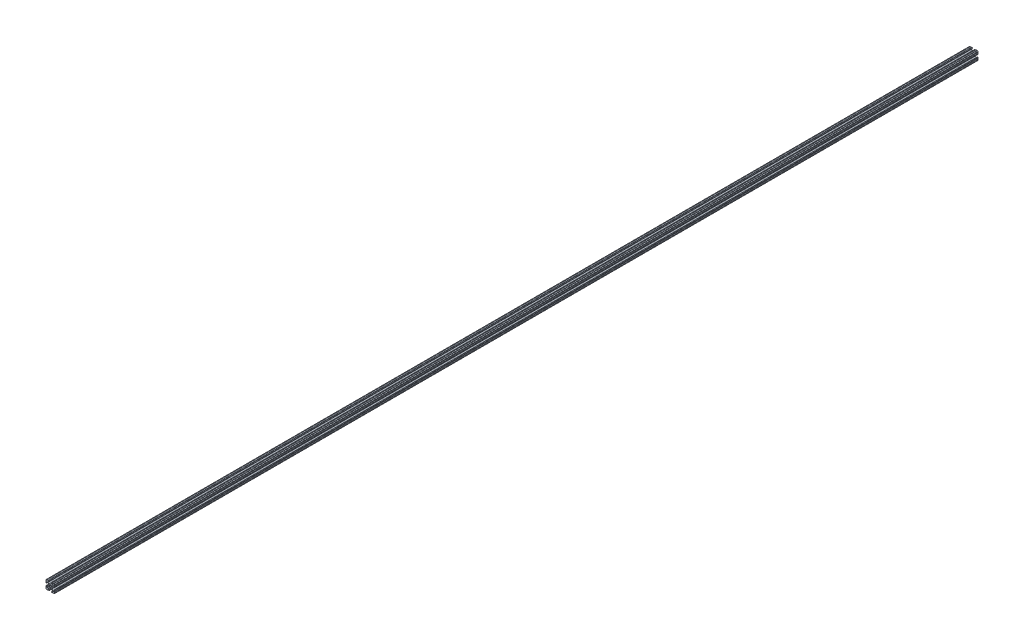
SolidWorks part; units mm, degrees
ref_plane "Front Plane" through (0, 0, 0) normal (0, 0, 1) x (1, 0, 0)
ref_plane "Top Plane" through (0, 0, 0) normal (0, 1, 0) x (1, 0, 0)
ref_plane "Right Plane" through (0, 0, 0) normal (1, 0, 0) x (0, 0, -1)
sketch "Sketch1" plane through (0, 0, 0) normal (0, 0, 1) x (1, 0, 0)
  line L0 (0, -12.7) -> (0, 12.7) construction
  line L1 (12.7, 0) -> (-12.7, 0) construction
  line L2 (3.2512, 12.7) -> (-3.2512, 12.7) construction
  line L3 (0, -4.5212) -> (0, 4.5212) construction
  line L4 (-3.2512, 12.7) -> (-3.2512, 10.4902) construction
  line L5 (12.7, -7.4168) -> (12.7, 7.4168) construction
  line L6 (0, -2.6035) -> (0, 2.6035) construction
  point P4 (0, 0)
  point P8 (0, 0)
  point P11 (0, 12.7)
  point P14 (0, 0)
  point P18 (12.7, 0)
  point P21 (0, 0)
sketch "Sketch2" plane through (0, 0, 0) normal (1, 0, 0) x (0, 0, -1)
  line L0 (-1371.6, 0) -> (1371.6, 0) construction
  point P4 (0, 0)
  dimension "Length" = 2743.2
sketch "Sketch3" plane through (0, 0, 0) normal (0, 0, 1) x (1, 0, 0)
  line L1 (12.7, -12.7) -> (-12.7, -12.7)
  line L2 (12.7, -12.7) -> (12.7, 12.7)
  line L3 (12.7, 12.7) -> (-12.7, 12.7)
  line L4 (-12.7, -12.7) -> (-12.7, 12.7)
  line L5 (12.7, -12.7) -> (-12.7, 12.7) construction
  line L6 (12.7, 12.7) -> (-12.7, -12.7) construction
  point P0 (0, 0)
extrude "Boss-Extrude1" add sketch "Sketch3" along normal up to vertex (1371.6 mm away) and the other way up to vertex (1371.6 mm away) up to point (0, 0, 1371.6) other way up to point (0, 0, -1371.6)
sketch "Sketch4" plane through (0, 0, 1371.6) normal (0, 0, 1) x (1, 0, 0)
  line L0 (-3.2512, 12.7) -> (-3.2512, 10.4902)
  line L1 (-3.2512, 10.4902) -> (-8.9276, 10.4902)
  line L2 (-8.9276, 10.4902) -> (-2.9586, 4.5212)
  line L3 (-2.9586, 4.5212) -> (2.9586, 4.5212)
  line L4 (0, -12.7) -> (0, 12.7) construction
  line L5 (12.7, 12.7) -> (-12.7, 12.7) construction
  line L6 (0, 12.7) -> (0, -12.7) construction
  line L7 (-12.7, 0) -> (12.7, 0) construction
  line L8 (-12.7, 12.7) -> (0, 0) construction
  line L9 (-12.7, 3.2512) -> (-10.4902, 3.2512)
  line L10 (-10.4902, 3.2512) -> (-10.4902, 8.9276)
  line L11 (-10.4902, 8.9276) -> (-4.5212, 2.9586)
  line L12 (-4.5212, 2.9586) -> (-4.5212, -2.9586)
  line L13 (4.5212, 2.9586) -> (4.5212, -2.9586)
  line L14 (10.4902, 8.9276) -> (4.5212, 2.9586)
  line L15 (10.4902, 3.2512) -> (10.4902, 8.9276)
  line L16 (12.7, 3.2512) -> (10.4902, 3.2512)
  line L17 (8.9276, 10.4902) -> (2.9586, 4.5212)
  line L18 (3.2512, 10.4902) -> (8.9276, 10.4902)
  line L19 (3.2512, 12.7) -> (3.2512, 10.4902)
  line L20 (3.2512, -12.7) -> (3.2512, -10.4902)
  line L21 (3.2512, -10.4902) -> (8.9276, -10.4902)
  line L22 (8.9276, -10.4902) -> (2.9586, -4.5212)
  line L23 (12.7, -3.2512) -> (10.4902, -3.2512)
  line L24 (10.4902, -3.2512) -> (10.4902, -8.9276)
  line L25 (10.4902, -8.9276) -> (4.5212, -2.9586)
  line L26 (-10.4902, -8.9276) -> (-4.5212, -2.9586)
  line L27 (-10.4902, -3.2512) -> (-10.4902, -8.9276)
  line L28 (-12.7, -3.2512) -> (-10.4902, -3.2512)
  line L29 (-2.9586, -4.5212) -> (2.9586, -4.5212)
  line L30 (-8.9276, -10.4902) -> (-2.9586, -4.5212)
  line L31 (-3.2512, -10.4902) -> (-8.9276, -10.4902)
  line L32 (-3.2512, -12.7) -> (-3.2512, -10.4902)
  line L33 (-12.7, 3.2512) -> (-12.7, -3.2512)
  line L34 (-3.2512, -12.7) -> (3.2512, -12.7)
  line L35 (12.7, -3.2512) -> (12.7, 3.2512)
  line L36 (3.2512, 12.7) -> (-3.2512, 12.7)
  line L37 (-12.7, 12.7) -> (-12.7, -12.7) construction
  line L38 (-12.7, -12.7) -> (12.7, -12.7) construction
  arc A3 (-6.3485, 10.4902) -> (-7.1039, 8.6665) centre (-6.3485, 9.4219) ccw
  arc A4 (7.1039, 8.6665) -> (6.3485, 10.4902) centre (6.3485, 9.4219) ccw
  arc A5 (8.6665, -7.1039) -> (10.4902, -6.3485) centre (9.4219, -6.3485) ccw
  arc A6 (10.4902, 6.3485) -> (8.6665, 7.1039) centre (9.4219, 6.3485) ccw
  arc A7 (-7.1039, -8.6665) -> (-6.3485, -10.4902) centre (-6.3485, -9.4219) ccw
  arc A8 (6.3485, -10.4902) -> (7.1039, -8.6665) centre (6.3485, -9.4219) ccw
  arc A9 (-8.6665, 7.1039) -> (-10.4902, 6.3485) centre (-9.4219, 6.3485) ccw
  arc A10 (-10.4902, -6.3485) -> (-8.6665, -7.1039) centre (-9.4219, -6.3485) ccw
  circle A11 centre (0, 0) radius 2.6035
  point P34 (0, 4.5212)
  point P45 (4.5212, 0)
  point P46 (-4.5212, 0)
  point P53 (0, -4.5212)
  point P81 (0, 0)
  line M2 (-12.7, 12.7) -> (-12.7, -12.7)
  line M3 (-12.7, -12.7) -> (12.7, -12.7)
  line M4 (12.7, -12.7) -> (12.7, 12.7)
  line M5 (12.7, 12.7) -> (-12.7, 12.7)
  dimension "D5" = 5.207
  dimension "D1" = 2.2098
  dimension "D2" = 2.2098
  dimension "D3" = 14.8336
  dimension "D4" = 4
extrude "Cut-Extrude1" cut sketch "Sketch4" against normal through all contours L17 A4 L18 L19 L0 L1 A3 L2 L3 M5 | L15 A6 L14 L13 L25 A5 L24 L23 L16 M4 | L21 A8 L22 L29 L30 A7 L31 L32 L20 M3 | L27 A10 L26 L12 L11 A9 L10 L9 L28 M2 | A11
sketch "Sketch5" plane through (0, 0, 1371.6) normal (0, 0, 1) x (1, 0, 0)
  line L0 (-4.3561, 12.7) -> (-3.2512, 12.7)
  line L1 (-3.2512, 12.7) -> (-3.2512, 10.4902)
  line L2 (-3.2512, 10.4902) -> (-4.3561, 10.4902)
  line L3 (0, -12.7) -> (0, 12.7) construction
  line L4 (-3.2512, 12.7) -> (-12.7, 12.7) construction
  line L5 (3.2512, 10.4902) -> (4.3561, 10.4902)
  line L6 (3.2512, 12.7) -> (3.2512, 10.4902)
  line L7 (4.3561, 12.7) -> (3.2512, 12.7)
  line L8 (12.7, 4.3561) -> (12.7, 3.2512)
  line L9 (12.7, 3.2512) -> (10.4902, 3.2512)
  line L10 (10.4902, 3.2512) -> (10.4902, 4.3561)
  line L11 (10.4902, -3.2512) -> (10.4902, -4.3561)
  line L12 (12.7, -3.2512) -> (10.4902, -3.2512)
  line L13 (12.7, -4.3561) -> (12.7, -3.2512)
  line L14 (4.3561, -12.7) -> (3.2512, -12.7)
  line L15 (3.2512, -12.7) -> (3.2512, -10.4902)
  line L16 (3.2512, -10.4902) -> (4.3561, -10.4902)
  line L17 (-3.2512, -10.4902) -> (-4.3561, -10.4902)
  line L18 (-3.2512, -12.7) -> (-3.2512, -10.4902)
  line L19 (-4.3561, -12.7) -> (-3.2512, -12.7)
  line L20 (-12.7, -4.3561) -> (-12.7, -3.2512)
  line L21 (-12.7, -3.2512) -> (-10.4902, -3.2512)
  line L22 (-10.4902, -3.2512) -> (-10.4902, -4.3561)
  line L23 (-10.4902, 3.2512) -> (-10.4902, 4.3561)
  line L24 (-12.7, 3.2512) -> (-10.4902, 3.2512)
  line L25 (-12.7, 4.3561) -> (-12.7, 3.2512)
  line L26 (-12.7, 12.7) -> (-12.7, 3.2512) construction
  line L27 (-10.7124, 12.7) -> (-9.6075, 12.7)
  line L28 (-6.3436, 12.7) -> (-5.2387, 12.7)
  line L29 (-12.7, 10.7124) -> (-12.7, 9.6075)
  line L30 (-12.7, 6.3436) -> (-12.7, 5.2387)
  line L31 (6.3437, 12.7) -> (5.2388, 12.7)
  line L32 (10.7125, 12.7) -> (9.6076, 12.7)
  line L33 (12.7, 10.7125) -> (12.7, 9.6075)
  line L34 (12.7, 6.3436) -> (12.7, 5.2387)
  line L35 (12.7, -6.3437) -> (12.7, -5.2388)
  line L36 (12.7, -10.7125) -> (12.7, -9.6076)
  line L37 (10.7125, -12.7) -> (9.6076, -12.7)
  line L38 (6.3437, -12.7) -> (5.2388, -12.7)
  line L39 (-6.3436, -12.7) -> (-5.2387, -12.7)
  line L40 (-10.7124, -12.7) -> (-9.6075, -12.7)
  line L41 (-12.7, -10.7125) -> (-12.7, -9.6076)
  line L42 (-12.7, -6.3437) -> (-12.7, -5.2388)
  line L43 (12.7, 12.7) -> (3.2512, 12.7) construction
  line L44 (12.7, 3.2512) -> (12.7, 12.7) construction
  arc A0 (-4.3561, 10.4902) -> (-4.3561, 12.7) centre (-4.3561, 11.5951) ccw
  arc A1 (4.3561, 10.4902) -> (4.3561, 12.7) centre (4.3561, 11.5951) cw
  arc A2 (10.4902, 4.3561) -> (12.7, 4.3561) centre (11.5951, 4.3561) ccw
  arc A3 (10.4902, -4.3561) -> (12.7, -4.3561) centre (11.5951, -4.3561) cw
  arc A4 (4.3561, -10.4902) -> (4.3561, -12.7) centre (4.3561, -11.5951) ccw
  arc A5 (-4.3561, -10.4902) -> (-4.3561, -12.7) centre (-4.3561, -11.5951) cw
  arc A6 (-10.4902, -4.3561) -> (-12.7, -4.3561) centre (-11.5951, -4.3561) ccw
  arc A7 (-10.4902, 4.3561) -> (-12.7, 4.3561) centre (-11.5951, 4.3561) cw
  arc A8 (-10.7124, 12.7) -> (-9.6075, 12.7) centre (-10.16, 12.7) ccw
  arc A9 (-6.3436, 12.7) -> (-5.2387, 12.7) centre (-5.7912, 12.7) ccw
  arc A10 (-12.7, 9.6075) -> (-12.7, 10.7124) centre (-12.7, 10.16) ccw
  arc A11 (-12.7, 5.2387) -> (-12.7, 6.3436) centre (-12.7, 5.7912) ccw
  arc A12 (5.2388, 12.7) -> (6.3437, 12.7) centre (5.7912, 12.7) ccw
  arc A13 (9.6076, 12.7) -> (10.7125, 12.7) centre (10.16, 12.7) ccw
  arc A14 (12.7, 10.7125) -> (12.7, 9.6075) centre (12.7, 10.16) ccw
  arc A15 (12.7, 6.3436) -> (12.7, 5.2387) centre (12.7, 5.7912) ccw
  arc A16 (12.7, -5.2388) -> (12.7, -6.3437) centre (12.7, -5.7912) ccw
  arc A17 (12.7, -9.6076) -> (12.7, -10.7125) centre (12.7, -10.16) ccw
  arc A18 (10.7125, -12.7) -> (9.6076, -12.7) centre (10.16, -12.7) ccw
  arc A19 (6.3437, -12.7) -> (5.2388, -12.7) centre (5.7912, -12.7) ccw
  arc A20 (-5.2387, -12.7) -> (-6.3436, -12.7) centre (-5.7912, -12.7) ccw
  arc A21 (-9.6075, -12.7) -> (-10.7124, -12.7) centre (-10.16, -12.7) ccw
  arc A22 (-12.7, -10.7125) -> (-12.7, -9.6076) centre (-12.7, -10.16) ccw
  arc A23 (-12.7, -6.3437) -> (-12.7, -5.2388) centre (-12.7, -5.7912) ccw
  point P11 (0, 0)
  point P52 (0, 0)
  point P104 (0, 0)
  line M5 (3.2512, -10.4902) -> (3.2512, -12.7)
  line M6 (3.2512, -12.7) -> (12.7, -12.7)
  line M7 (12.7, -12.7) -> (12.7, -3.2512)
  line M8 (12.7, -3.2512) -> (10.4902, -3.2512)
  line M9 (10.4902, -3.2512) -> (10.4902, -6.3485)
  line M15 (10.4902, 6.3485) -> (10.4902, 3.2512)
  line M16 (10.4902, 3.2512) -> (12.7, 3.2512)
  line M17 (12.7, 3.2512) -> (12.7, 12.7)
  line M18 (12.7, 12.7) -> (3.2512, 12.7)
  line M19 (3.2512, 12.7) -> (3.2512, 10.4902)
  line M20 (3.2512, 10.4902) -> (6.3485, 10.4902)
  line M26 (-6.3485, 10.4902) -> (-3.2512, 10.4902)
  line M27 (-3.2512, 10.4902) -> (-3.2512, 12.7)
  line M28 (-3.2512, 12.7) -> (-12.7, 12.7)
  line M29 (-12.7, 12.7) -> (-12.7, 3.2512)
  line M30 (-12.7, 3.2512) -> (-10.4902, 3.2512)
  line M31 (-10.4902, 3.2512) -> (-10.4902, 6.3485)
  line M37 (-10.4902, -6.3485) -> (-10.4902, -3.2512)
  line M38 (-10.4902, -3.2512) -> (-12.7, -3.2512)
  line M39 (-12.7, -3.2512) -> (-12.7, -12.7)
  line M40 (-12.7, -12.7) -> (-3.2512, -12.7)
  line M41 (-3.2512, -12.7) -> (-3.2512, -10.4902)
  line M42 (-3.2512, -10.4902) -> (-6.3485, -10.4902)
  line M48 (6.3485, -10.4902) -> (3.2512, -10.4902)
  dimension "D2" = 0.5524
  dimension "D3" = 2.54
  dimension "D4" = 2.54
  dimension "D5" = 2.54
  dimension "D6" = 2.54
  dimension "D1" = 4
  dimension "D7" = 4
extrude "Cut-Extrude2" cut sketch "Sketch5" against normal through all contours A7 M30 M29 | A7 L24 M31 | A6 L21 M39 | A6 M37 M38 | A5 L18 M42 | A5 M41 M40 | A4 M48 M5 | A4 L15 M6 | A3 L12 M9 | A3 M8 M7 | A2 M15 M16 | A2 L9 M17 | A1 M19 M18 | A1 L6 M20 | A0 L1 M28 | A0 M26 M27 | A11 L30 | A10 L29 | A8 L27 | A9 L28 | L31 A12 | L32 A13 | L33 A14 | L34 A15 | L42 A23 | L41 A22 | L40 A21 | L39 A20 | L36 A17 | L35 A16 | L37 A18 | L38 A19
fillet "Fillet1" radius 2.54 8 edges at (2.9586, -4.5212, 0) (-2.9586, -4.5212, 0) (4.5212, -2.9586, 0) (4.5212, 2.9586, 0) (-2.9586, 4.5212, 0) (2.9586, 4.5212, 0) (-4.5212, -2.9586, 0) (-4.5212, 2.9586, 0)
fillet "Fillet2" radius 1.778 4 edges at (12.7, -12.7, 0) (12.7, 12.7, 0) (-12.7, -12.7, 0) (-12.7, 12.7, 0)
equation "\"D2@Sketch4\"=\"Thickness@Sketch1\""
equation "\"D1@Sketch4\"=\"Thickness@Sketch1\""
equation "\"D3@Sketch4\"=\"Opening Width@Sketch1\""
equation "\"D5@Sketch4\"=\"Hole Dia@Sketch1\""
equation "\"D2@Sketch5\"=\"Thickness@Sketch1\"/4"
equation "\"D3@Sketch5\"=\"Height@Sketch1\"/10"
equation "\"D4@Sketch5\"=\"D3@Sketch5\""
equation "\"D5@Sketch5\"=\"D4@Sketch5\""
equation "\"D6@Sketch5\"=\"D5@Sketch5\""
